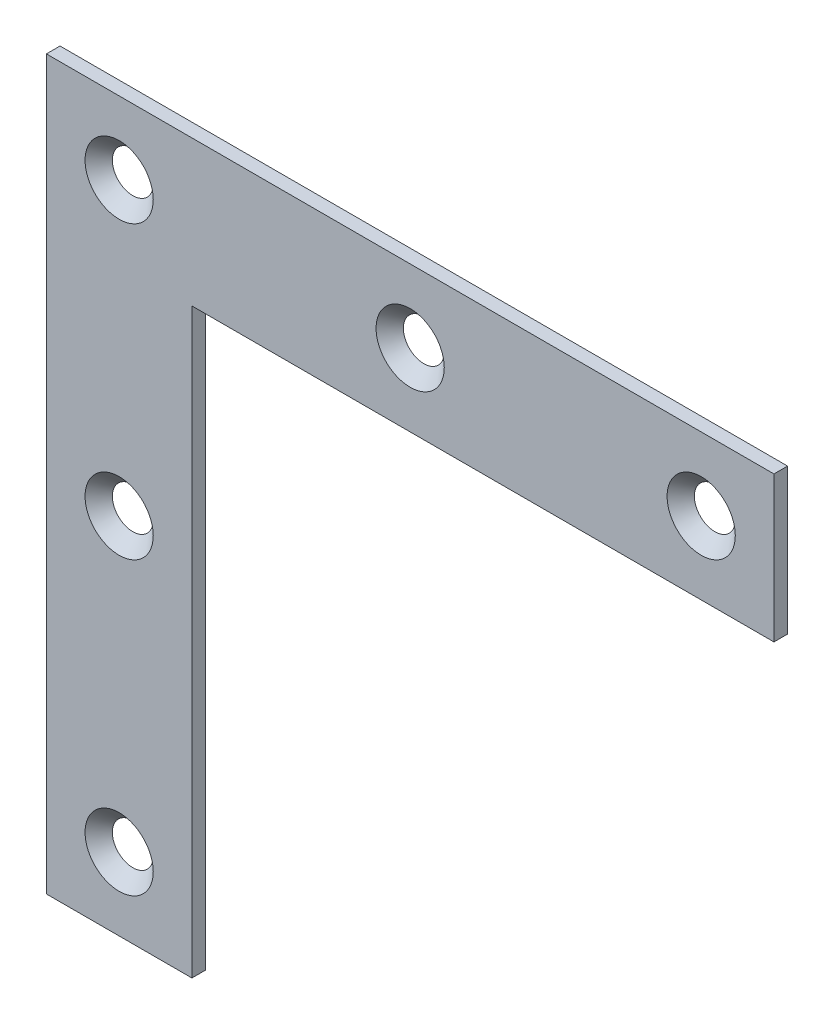
SolidWorks part; units mm, degrees
ref_plane "Front Plane" through (0, 0, 0) normal (0, 0, 1) x (1, 0, 0)
ref_plane "Top Plane" through (0, 0, 0) normal (0, 1, 0) x (1, 0, 0)
ref_plane "Right Plane" through (0, 0, 0) normal (1, 0, 0) x (0, 0, -1)
ref_plane "Plane1" through (0, 0, 1.5) normal (0, 0, 1) x (1, 0, 0)
sketch "Sketch1" plane through (0, 0, 1.5) normal (0, 0, 1) x (1, 0, 0)
  line L0 (0, 0) -> (0, -80)
  line L1 (0, -80) -> (80, -80)
  line L2 (80, -80) -> (80, 0)
  line L3 (80, 0) -> (0, 0)
extrude "Boss-Extrude1" add sketch "Sketch1" against normal blind 1.5
sketch "Sketch2" plane through (0, 0, 0) normal (0, 0, -1) x (-1, 0, 0)
  line L0 (-16, -80) -> (-16, -16)
  line L1 (-16, -16) -> (-80, -16)
  line L2 (-80, -16) -> (-80, -80)
  line L3 (-80, -80) -> (-16, -80)
extrude "Cut-Extrude1" cut sketch "Sketch2" against normal through all
hole_wizard "Hole1" positions "Sketch4" profile "Sketch3" legacy
sketch "Sketch4" plane through (0, 0, 1.5) normal (0, 0, 1) x (1, 0, 0)
  point P0 (8, -8)
  point P1 (40, -8)
  point P2 (72, -8)
  point P3 (8, -40)
  point P4 (8, -72)
sketch "Sketch3" plane through (8, -8, 1.5) normal (1, 0, 0) x (0, -1, 0)
  line L0 (0, 0) -> (0, 1.5)
  line L1 (0, 1.5) -> (2.25, 1.5)
  line L2 (2.25, 1.5) -> (3.75, 0)
  line L3 (3.75, 0) -> (0, 0)
  line L4 (0, 110) -> (0, -10) construction
  dimension "Minor Diameter" = 4.5
  dimension "Depth" = 1.5
  dimension "Major Diameter" = 7.5
